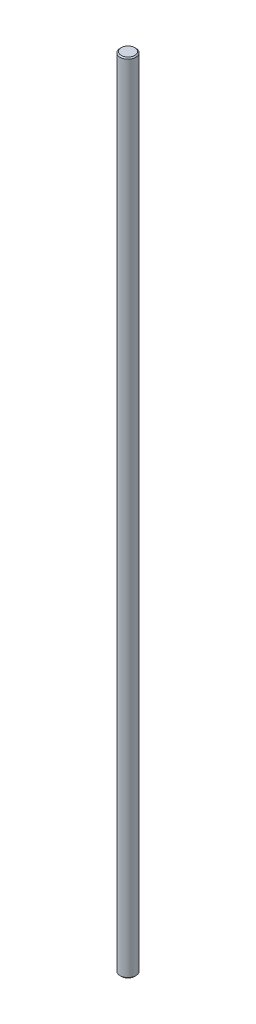
SolidWorks part; units mm, degrees
ref_plane "Plan de face" through (0, 0, 0) normal (0, 0, 1) x (1, 0, 0)
ref_plane "Plan de dessus" through (0, 0, 0) normal (0, 1, 0) x (1, 0, 0)
ref_plane "Plan de droite" through (0, 0, 0) normal (1, 0, 0) x (0, 0, -1)
sketch "Esquisse1" plane through (0, 0, 0) normal (0, 1, 0) x (1, 0, 0)
  circle A0 centre (0, 0) radius 7
extrude "Boss.-Extru.1" add sketch "Esquisse1" along normal blind 710
chamfer "Chanfrein1" distance 1 angle 45 2 edges at (0, 0, 7) (0, 710, 7)
sketch "Esquisse2" plane through (0, 0, 0) normal (0, 0, 1) x (1, 0, 0)
  line L0 (0, 709) -> (0, 0) construction
  line L1 (-7, 709) -> (7, 709) construction
  line L2 (40.7414, 354.5) -> (-36.2643, 354.5) construction
  line L3 (-4, 473) -> (-4, 236)
  line L4 (4, 236) -> (4, 473)
  line L5 (40.7414, 473) -> (-36.2643, 473) construction
  line L6 (40.7414, 236) -> (-36.2643, 236) construction
  arc A0 (4, 473) -> (-4, 473) centre (0, 473) ccw
  arc A1 (-4, 236) -> (4, 236) centre (0, 236) ccw
  point P7 (-4, 709)
  point P8 (-4, 0)
  point P9 (4, 709)
  point P10 (4, 0)
  dimension "D3" = 118.5
  dimension "D4" = 118.5
extrude "Enlèv. mat.-Extru.1" cut sketch "Esquisse2" against normal blind 10 from offset 1
